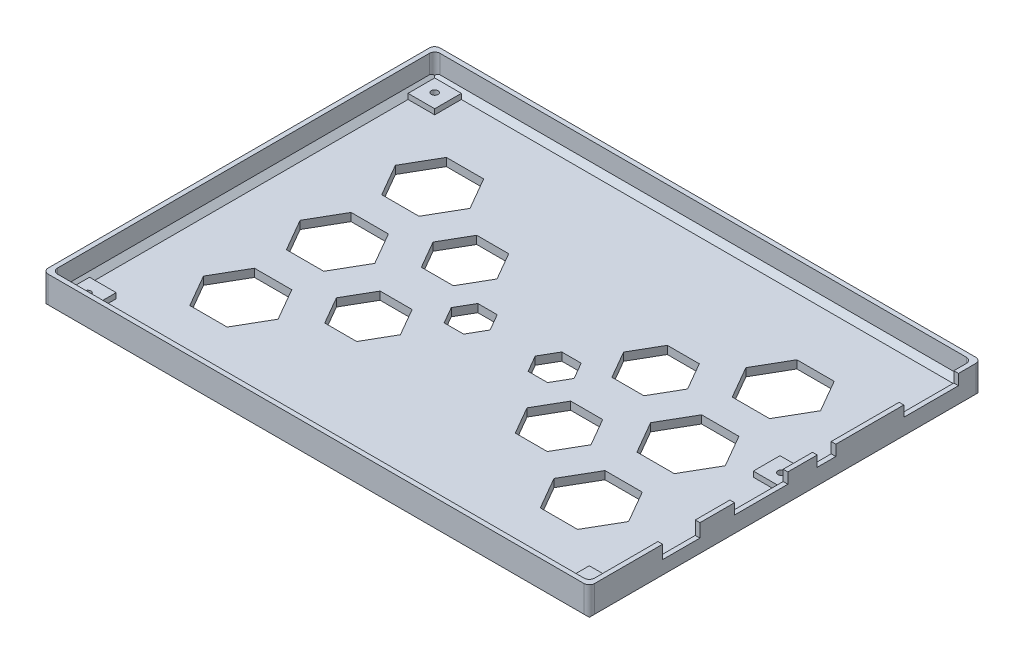
SolidWorks part; units mm, degrees
ref_plane "Front Plane" through (0, 0, 0) normal (0, 0, 1) x (1, 0, 0)
ref_plane "Top Plane" through (0, 0, 0) normal (0, 1, 0) x (1, 0, 0)
ref_plane "Right Plane" through (0, 0, 0) normal (1, 0, 0) x (0, 0, -1)
sketch "Sketch1" plane through (0, 0, 0) normal (0, 1, 0) x (1, 0, 0)
  line L1 (102.5, -73.5) -> (-102.5, -73.5)
  line L2 (102.5, -73.5) -> (102.5, 73.5)
  line L3 (102.5, 73.5) -> (-102.5, 73.5)
  line L4 (-102.5, -73.5) -> (-102.5, 73.5)
  line L5 (102.5, -73.5) -> (-102.5, 73.5) construction
  line L6 (102.5, 73.5) -> (-102.5, -73.5) construction
  point P0 (0, 0)
  dimension "D1" = 147
  dimension "D2" = 205
extrude "Boss-Extrude1" add sketch "Sketch1" along normal blind 12
sketch "Sketch2" plane through (0, 12, 0) normal (0, 1, 0) x (1, 0, 0)
  line L1 (100.75, -71.75) -> (-100.75, -71.75)
  line L2 (100.75, -71.75) -> (100.75, 71.75)
  line L3 (100.75, 71.75) -> (-100.75, 71.75)
  line L4 (-100.75, -71.75) -> (-100.75, 71.75)
  line L5 (100.75, -71.75) -> (-100.75, 71.75) construction
  line L6 (100.75, 71.75) -> (-100.75, -71.75) construction
  point P0 (0, 0)
  dimension "D1" = 201.5
  dimension "D2" = 143.5
extrude "Cut-Extrude1" cut sketch "Sketch2" against normal blind 9
sketch "Sketch3" plane through (0, 3, 0) normal (0, 1, 0) x (1, 0, 0)
  line L0 (100.75, 71.75) -> (-100.75, 71.75) construction
  line L1 (0, 0) -> (0, 68.0662) construction
  line L2 (23.0335, 0.25) -> (19.3917, 6.5577)
  line L3 (19.3917, 6.5577) -> (12.1083, 6.5577)
  line L4 (12.1083, 6.5577) -> (8.4665, 0.25)
  line L5 (8.4665, 0.25) -> (12.1083, -6.0577)
  line L6 (12.1083, -6.0577) -> (19.3917, -6.0577)
  line L7 (47.75, 18.125) -> (41.75, 28.5173)
  line L8 (41.75, 28.5173) -> (29.75, 28.5173)
  line L9 (29.75, 28.5173) -> (23.75, 18.125)
  line L10 (23.75, 18.125) -> (29.75, 7.7327)
  line L11 (29.75, 7.7327) -> (41.75, 7.7327)
  line L12 (41.75, 7.7327) -> (47.75, 18.125)
  line L13 (47.75, -18.12) -> (41.75, -7.7277)
  line L14 (41.75, -7.7277) -> (29.75, -7.7277)
  line L15 (29.75, -7.7277) -> (23.75, -18.12)
  line L16 (23.75, -18.12) -> (29.75, -28.5123)
  line L17 (29.75, -28.5123) -> (41.75, -28.5123)
  line L18 (41.75, -28.5123) -> (47.75, -18.12)
  line L19 (79.75, 0.25) -> (72.75, 12.3744)
  line L20 (72.75, 12.3744) -> (58.75, 12.3744)
  line L21 (58.75, 12.3744) -> (51.75, 0.25)
  line L22 (51.75, 0.25) -> (58.75, -11.8744)
  line L23 (58.75, -11.8744) -> (72.75, -11.8744)
  line L24 (72.75, -11.8744) -> (79.75, 0.25)
  line L25 (79.75, -36) -> (72.75, -23.8756)
  line L26 (72.75, -23.8756) -> (58.75, -23.8756)
  line L27 (58.75, -23.8756) -> (51.75, -36)
  line L28 (51.75, -36) -> (58.75, -48.1244)
  line L29 (58.75, -48.1244) -> (72.75, -48.1244)
  line L30 (72.75, -48.1244) -> (79.75, -36)
  line L31 (79.75, 36) -> (72.75, 48.1244)
  line L32 (72.75, 48.1244) -> (58.75, 48.1244)
  line L33 (58.75, 48.1244) -> (51.75, 36)
  line L34 (51.75, 36) -> (58.75, 23.8756)
  line L35 (58.75, 23.8756) -> (72.75, 23.8756)
  line L36 (72.75, 23.8756) -> (79.75, 36)
  line L37 (100.75, -71.75) -> (100.75, 71.75) construction
  line L38 (-100.75, -71.75) -> (100.75, -71.75) construction
  line L39 (100.75, 71.75) -> (-100.75, 71.75) construction
  line L40 (19.3917, -6.0577) -> (23.0335, 0.25)
  line L41 (-19.3917, -6.0577) -> (-23.0335, 0.25)
  line L42 (-72.75, 23.8756) -> (-79.75, 36)
  line L43 (-58.75, 23.8756) -> (-72.75, 23.8756)
  line L44 (-51.75, 36) -> (-58.75, 23.8756)
  line L45 (-58.75, 48.1244) -> (-51.75, 36)
  line L46 (-72.75, 48.1244) -> (-58.75, 48.1244)
  line L47 (-79.75, 36) -> (-72.75, 48.1244)
  line L48 (-72.75, -48.1244) -> (-79.75, -36)
  line L49 (-58.75, -48.1244) -> (-72.75, -48.1244)
  line L50 (-51.75, -36) -> (-58.75, -48.1244)
  line L51 (-58.75, -23.8756) -> (-51.75, -36)
  line L52 (-72.75, -23.8756) -> (-58.75, -23.8756)
  line L53 (-79.75, -36) -> (-72.75, -23.8756)
  line L54 (-72.75, -11.8744) -> (-79.75, 0.25)
  line L55 (-58.75, -11.8744) -> (-72.75, -11.8744)
  line L56 (-51.75, 0.25) -> (-58.75, -11.8744)
  line L57 (-58.75, 12.3744) -> (-51.75, 0.25)
  line L58 (-72.75, 12.3744) -> (-58.75, 12.3744)
  line L59 (-79.75, 0.25) -> (-72.75, 12.3744)
  line L60 (-41.75, -28.5123) -> (-47.75, -18.12)
  line L61 (-29.75, -28.5123) -> (-41.75, -28.5123)
  line L62 (-23.75, -18.12) -> (-29.75, -28.5123)
  line L63 (-29.75, -7.7277) -> (-23.75, -18.12)
  line L64 (-41.75, -7.7277) -> (-29.75, -7.7277)
  line L65 (-47.75, -18.12) -> (-41.75, -7.7277)
  line L66 (-41.75, 7.7327) -> (-47.75, 18.125)
  line L67 (-29.75, 7.7327) -> (-41.75, 7.7327)
  line L68 (-23.75, 18.125) -> (-29.75, 7.7327)
  line L69 (-29.75, 28.5173) -> (-23.75, 18.125)
  line L70 (-41.75, 28.5173) -> (-29.75, 28.5173)
  line L71 (-47.75, 18.125) -> (-41.75, 28.5173)
  line L72 (-12.1083, -6.0577) -> (-19.3917, -6.0577)
  line L73 (-8.4665, 0.25) -> (-12.1083, -6.0577)
  line L74 (-12.1083, 6.5577) -> (-8.4665, 0.25)
  line L75 (-19.3917, 6.5577) -> (-12.1083, 6.5577)
  line L76 (-23.0335, 0.25) -> (-19.3917, 6.5577)
  circle A0 centre (15.75, 0.25) radius 6.3077 construction
  circle A1 centre (35.75, 18.125) radius 10.3923 construction
  circle A2 centre (35.75, -18.12) radius 10.3923 construction
  circle A3 centre (65.75, 0.25) radius 12.1244 construction
  circle A4 centre (65.75, -36) radius 12.1244 construction
  circle A5 centre (65.75, 36) radius 12.1244 construction
  circle A6 centre (-65.75, 36) radius 12.1244 construction
  circle A7 centre (-65.75, -36) radius 12.1244 construction
  circle A8 centre (-65.75, 0.25) radius 12.1244 construction
  circle A9 centre (-35.75, -18.12) radius 10.3923 construction
  circle A10 centre (-35.75, 18.125) radius 10.3923 construction
  circle A11 centre (-15.75, 0.25) radius 6.3077 construction
  dimension "D1" = 71.5
  dimension "D2" = 35.75
  dimension "D3" = 35.75
  dimension "D4" = 14
  dimension "D5" = 14
  dimension "D6" = 14
  dimension "D7" = 35
  dimension "D8" = 12
  dimension "D9" = 12
  dimension "D10" = 53.625
  dimension "D11" = 53.63
  dimension "D12" = 30
  dimension "D13" = 20
extrude "Cut-Extrude2" cut sketch "Sketch3" against normal through all
chamfer "Chamfer1" distance 2 angle 45 8 edges at (100.75, 3, 0) (0, 3, 71.75) (-100.75, 3, 0) (0, 3, -71.75) (-102.5, 0, 0) (0, 0, -73.5) (102.5, 0, 0) (0, 0, 73.5)
fillet "Fillet1" radius 2 8 edges at (100.75, 8.5, 71.75) (100.75, 8.5, -71.75) (-100.75, 8.5, -71.75) (-100.75, 8.5, 71.75) (102.5, 7, 73.5) (102.5, 7, -73.5) (-102.5, 7, -73.5) (-102.5, 7, 73.5)
sketch "Sketch4" plane through (102.5, 0, 0) normal (1, 0, 0) x (0, 0, -1)
  line L1 (-46, 12) -> (-32, 12)
  line L2 (-46, 12) -> (-46, 7)
  line L3 (-46, 7) -> (-32, 7)
  line L4 (-32, 12) -> (-32, 7)
  line L5 (-46, 12) -> (-32, 7) construction
  line L6 (-46, 7) -> (-32, 12) construction
  line L7 (71.5, 0) -> (-71.5, 0) construction
  line L8 (-71.5, 12) -> (71.5, 12) construction
  line L9 (-73.5, 2) -> (-73.5, 12) construction
  line L10 (73.5, 12) -> (73.5, 2) construction
  line L11 (-19, 12) -> (1, 12)
  line L12 (-19, 12) -> (-19, 8)
  line L13 (-19, 8) -> (1, 8)
  line L14 (1, 12) -> (1, 8)
  line L15 (-19, 12) -> (1, 8) construction
  line L16 (-19, 8) -> (1, 12) construction
  line L17 (12, 12) -> (19, 12)
  line L18 (12, 12) -> (12, 8)
  line L19 (12, 8) -> (19, 8)
  line L20 (19, 12) -> (19, 8)
  line L21 (12, 12) -> (19, 8) construction
  line L22 (12, 8) -> (19, 12) construction
  line L23 (44.5, 12) -> (65, 12)
  line L24 (44.5, 12) -> (44.5, 8)
  line L25 (44.5, 8) -> (65, 8)
  line L26 (65, 12) -> (65, 8)
  line L27 (44.5, 12) -> (65, 8) construction
  line L28 (44.5, 8) -> (65, 12) construction
  point P0 (-39, 9.5)
  point P11 (-9, 10)
  point P16 (15.5, 10)
  point P21 (54.75, 10)
  dimension "D1" = 14
  dimension "D2" = 7
  dimension "D3" = 27.5
  dimension "D4" = 20
  dimension "D5" = 8
  dimension "D6" = 13
  dimension "D7" = 7
  dimension "D8" = 8
  dimension "D9" = 11
  dimension "D10" = 20.5
  dimension "D11" = 8
  dimension "D12" = 8.5
extrude "Cut-Extrude3" cut sketch "Sketch4" against normal blind 10
sketch "Sketch5" plane through (0, 3, 0) normal (0, 1, 0) x (1, 0, 0)
  line L0 (-98.75, 69.75) -> (-98.75, -69.75) construction
  line L1 (-88.75, 59.75) -> (-98.75, 59.75)
  line L2 (-88.75, 59.75) -> (-88.75, 69.75)
  line L3 (-88.75, 69.75) -> (-98.75, 69.75)
  line L4 (-98.75, 59.75) -> (-98.75, 69.75)
  line L5 (-88.75, 59.75) -> (-98.75, 69.75) construction
  line L6 (-88.75, 69.75) -> (-98.75, 59.75) construction
  line L7 (-88.75, -59.75) -> (-98.75, -59.75)
  line L8 (-88.75, -59.75) -> (-88.75, -69.75)
  line L9 (-88.75, -69.75) -> (-98.75, -69.75)
  line L10 (-98.75, -59.75) -> (-98.75, -69.75)
  line L11 (-88.75, -59.75) -> (-98.75, -69.75) construction
  line L12 (-88.75, -69.75) -> (-98.75, -59.75) construction
  line L13 (98.75, -59.75) -> (88.75, -59.75)
  line L14 (98.75, -59.75) -> (98.75, -69.75)
  line L15 (98.75, -69.75) -> (88.75, -69.75)
  line L16 (88.75, -59.75) -> (88.75, -69.75)
  line L17 (98.75, -59.75) -> (88.75, -69.75) construction
  line L18 (98.75, -69.75) -> (88.75, -59.75) construction
  line L19 (98.75, 11.7967) -> (88.75, 11.7967)
  line L20 (98.75, 11.7967) -> (98.75, 1.7967)
  line L21 (98.75, 1.7967) -> (88.75, 1.7967)
  line L22 (88.75, 11.7967) -> (88.75, 1.7967)
  line L23 (98.75, 11.7967) -> (88.75, 1.7967) construction
  line L24 (98.75, 1.7967) -> (88.75, 11.7967) construction
  line L25 (98.75, 69.75) -> (-98.75, 69.75) construction
  line L26 (-98.75, -69.75) -> (98.75, -69.75) construction
  line L27 (98.75, -69.75) -> (98.75, 69.75) construction
  point P0 (-93.75, 64.75)
  point P5 (-93.75, -64.75)
  point P10 (93.75, -64.75)
  point P15 (93.75, 6.7967)
  point P28 (91.25, 10.0734)
  point P29 (91.25, 11.8762)
  point P30 (91.25, 6.3872)
  point P31 (93.75, 6.7967)
  dimension "D1" = 10
  dimension "D2" = 10
  dimension "D3" = 10
  dimension "D4" = 10
  dimension "D5" = 10
  dimension "D6" = 10
  dimension "D7" = 10
  dimension "D8" = 10
extrude "Boss-Extrude2" add sketch "Sketch5" along normal blind 2
sketch "Sketch6" plane through (0, 5, 0) normal (0, 1, 0) x (1, 0, 0)
  line L0 (100.5, 73.5) -> (-100.5, 73.5) construction
  line L1 (-102.5, 71.5) -> (-102.5, -71.5) construction
  line L2 (-100.5, -73.5) -> (100.5, -73.5) construction
  line L3 (102.5, -71.5) -> (102.5, -46) construction
  circle A0 centre (-94, -65.2) radius 1.25
  circle A1 centre (-94, 65) radius 1.25
  circle A2 centre (94.5, 6.5) radius 1.25
  circle A3 centre (94.5, -65.2) radius 1.25
  point P12 (0, 0)
  point P17 (0, 0)
  point P18 (0, 0)
  dimension "D1" = 2.5
  dimension "D2" = 2.5
  dimension "D3" = 2.5
  dimension "D4" = 2.5
  dimension "D9" = 67
  dimension "D5" = 8.5
  dimension "D6" = 8.5
  dimension "D7" = 8.3
  dimension "D8" = 8
extrude "Cut-Extrude4" cut sketch "Sketch6" against normal blind 3
